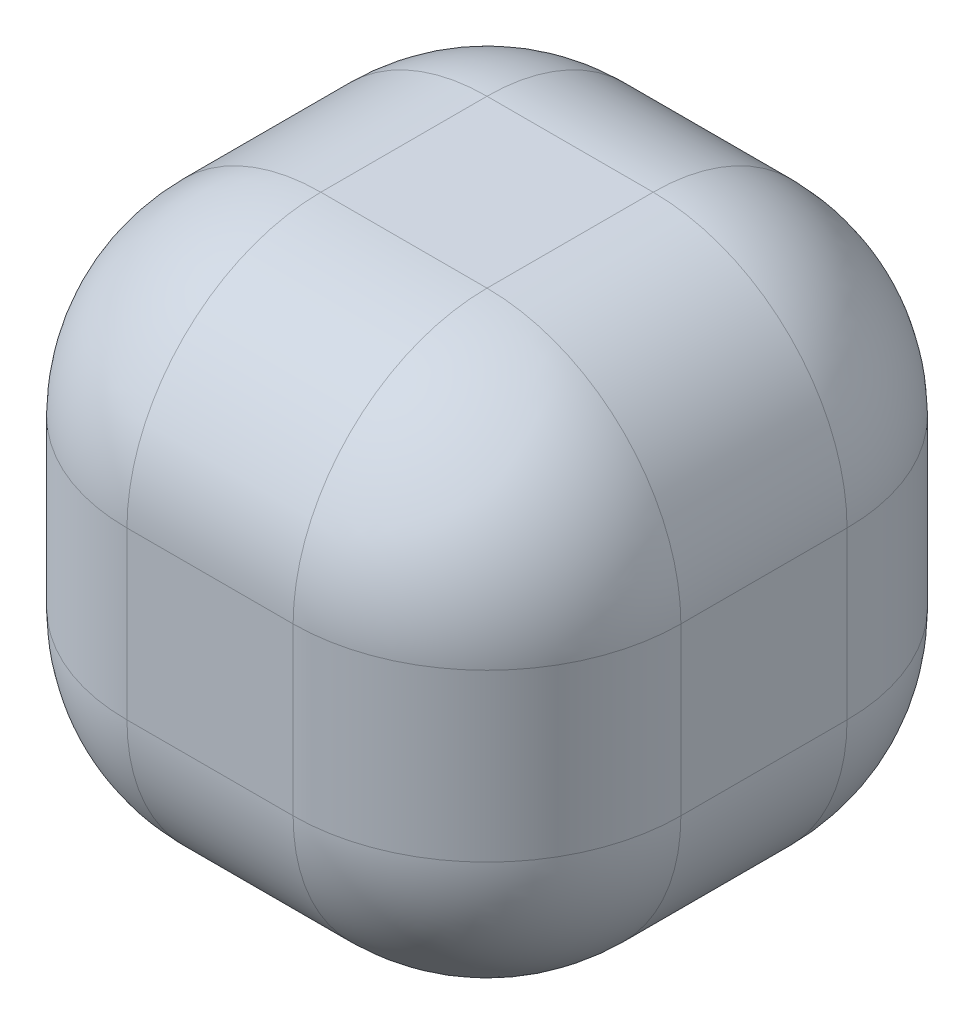
SolidWorks part; units mm, degrees
ref_plane "Front Plane" through (0, 0, 0) normal (0, 0, 1) x (1, 0, 0)
ref_plane "Top Plane" through (0, 0, 0) normal (0, 1, 0) x (1, 0, 0)
ref_plane "Right Plane" through (0, 0, 0) normal (1, 0, 0) x (0, 0, -1)
sketch "Sketch1" plane through (0, 0, 0) normal (0, 1, 0) x (1, 0, 0)
  line L1 (-20, -20) -> (20, -20)
  line L2 (-20, -20) -> (-20, 20)
  line L3 (-20, 20) -> (20, 20)
  line L4 (20, -20) -> (20, 20)
  line L5 (-20, -20) -> (20, 20) construction
  line L6 (-20, 20) -> (20, -20) construction
  point P0 (0, 0)
  dimension "D1" = 40
  dimension "D2" = 40
extrude "Boss-Extrude1" add sketch "Sketch1" along normal blind 40
fillet "Fillet1" radius 14 12 edges at (-20, 20, -20) (20, 20, -20) (20, 20, 20) (-20, 20, 20) (-20, 40, 0) (0, 40, 20) (20, 40, 0) (0, 40, -20) (-20, 0, 0) (0, 0, -20) (20, 0, 0) (0, 0, 20)
sketch3d "URDF Reference"
  line L0 (0, 0, 0) -> (10, 0, 0) construction
  line L1 (0, 0, 0) -> (0, 0, -10) construction
  point P0 (0, 0, 0)
  point P1 (0, 0, 0)
